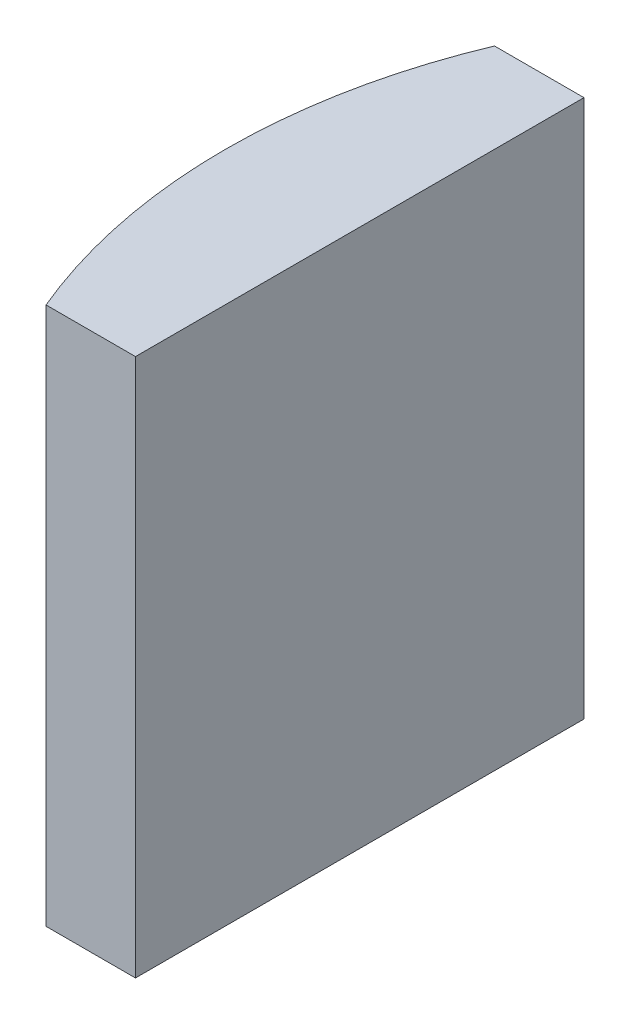
SolidWorks part; units mm, degrees
ref_plane "前视基准面" through (0, 0, 0) normal (0, 0, 1) x (1, 0, 0)
ref_plane "上视基准面" through (0, 0, 0) normal (0, 1, 0) x (1, 0, 0)
ref_plane "右视基准面" through (0, 0, 0) normal (1, 0, 0) x (0, 0, -1)
sketch "草图1" plane through (0, 0, 0) normal (0, 1, 0) x (1, 0, 0)
  line L0 (10.7432, 0) -> (-9.7696, 0) construction
  line L1 (-7.5689, 5) -> (-5.5748, 5)
  line L2 (-7.5689, -5) -> (-5.5748, -5)
  line L3 (-5.5748, 5) -> (-5.5748, -5)
  arc A0 (-7.5689, 5) -> (-7.5689, -5) centre (4.3552, 0) ccw
  point P19 (-8.5748, 0)
  point P20 (-5.5748, 0)
  dimension "D2" = 5
  dimension "D3" = 12.93
  dimension "D4" = 3
  dimension "D1" = 5
extrude "凸台-拉伸1" add sketch "草图1" along normal blind 12
